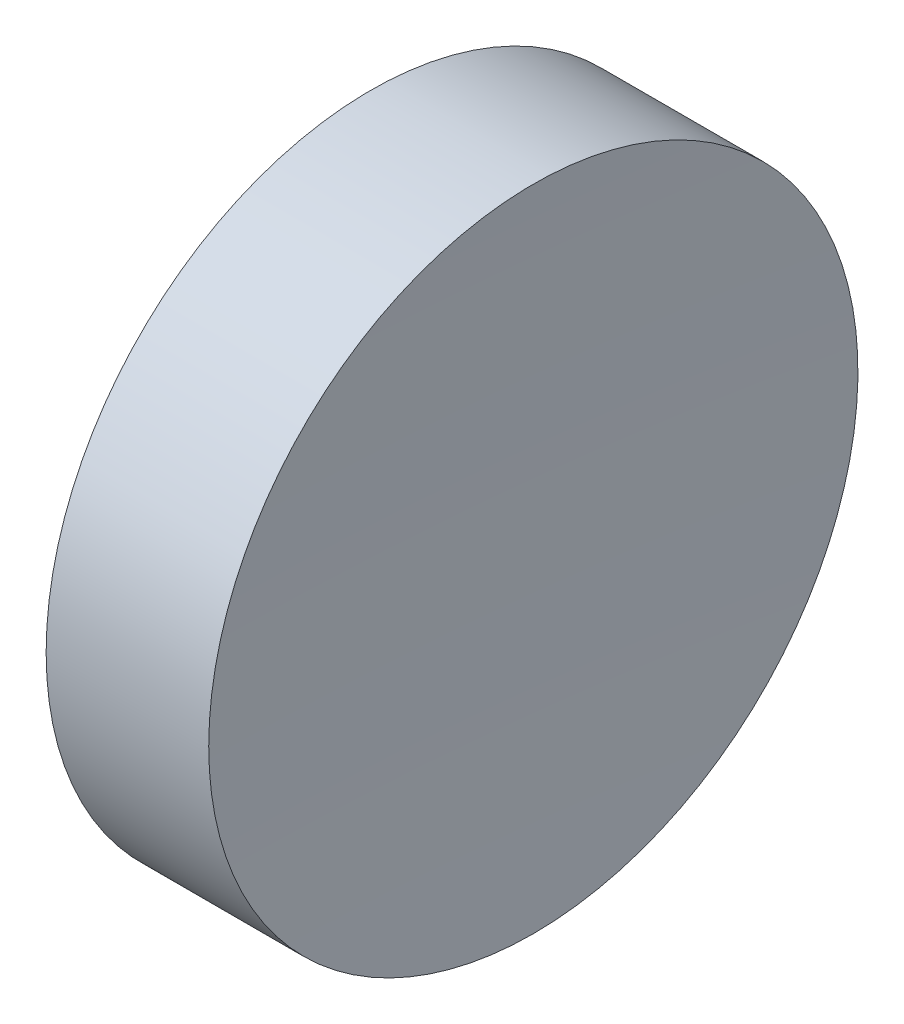
SolidWorks part; units mm, degrees
ref_plane "前视基准面" through (0, 0, 0) normal (0, 0, 1) x (1, 0, 0)
ref_plane "上视基准面" through (0, 0, 0) normal (0, 1, 0) x (1, 0, 0)
ref_plane "右视基准面" through (0, 0, 0) normal (1, 0, 0) x (0, 0, -1)
sketch "草图1" plane through (0, 0, 0) normal (0, 0, 1) x (1, 0, 0)
  line L0 (108.9851, 69.378) -> (132.7763, 69.378) construction
  line L1 (115.0927, 69.378) -> (115.0927, 81.878)
  line L2 (115.0927, 81.878) -> (121.3532, 81.878)
  line L3 (121.0927, 69.378) -> (115.0927, 69.378)
  arc A0 (121.3532, 81.878) -> (121.0927, 69.378) centre (421.0927, 69.378) ccw
revolve "旋转1" add sketch "草图1" angle 360 about L0
